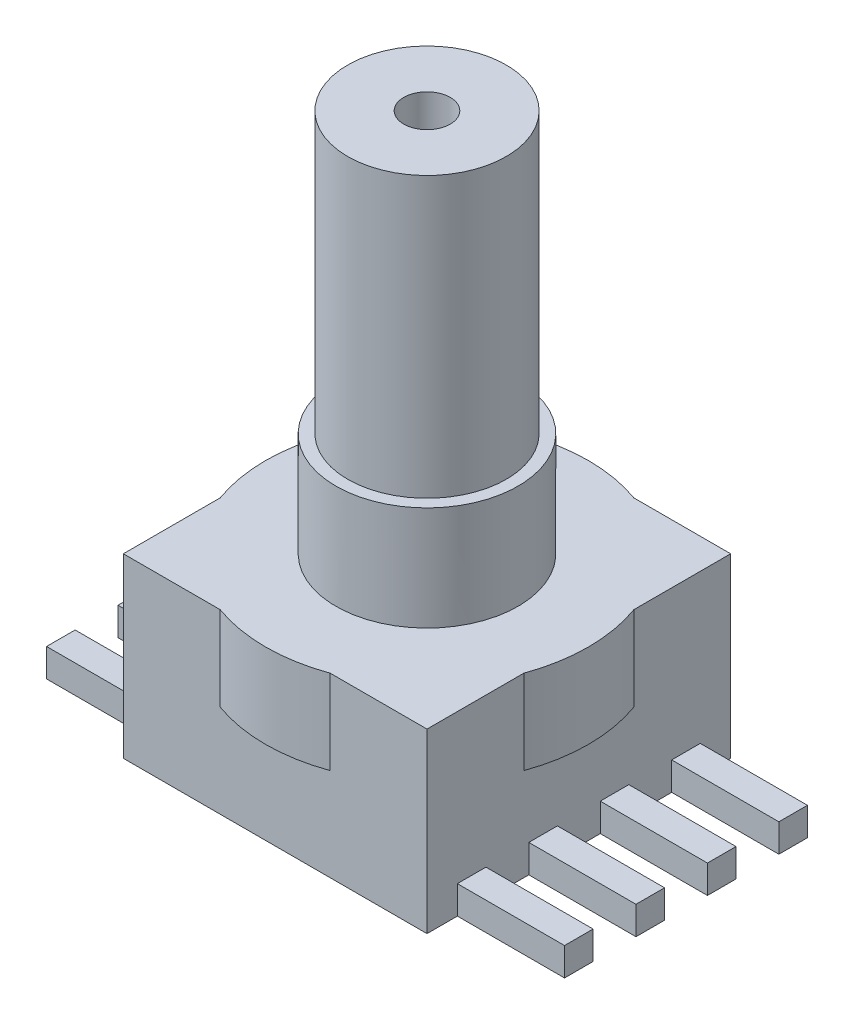
SolidWorks part; units mm, degrees
ref_plane "Front Plane" through (0, 0, 0) normal (0, 0, 1) x (1, 0, 0)
ref_plane "Top Plane" through (0, 0, 0) normal (0, 1, 0) x (1, 0, 0)
ref_plane "Right Plane" through (0, 0, 0) normal (1, 0, 0) x (0, 0, -1)
sketch "Sketch1" plane through (0, 0, 0) normal (0, 1, 0) x (1, 0, 0)
  line L1 (-5.3975, -5.3975) -> (5.3975, -5.3975)
  line L2 (-5.3975, -5.3975) -> (-5.3975, 5.3975)
  line L3 (-5.3975, 5.3975) -> (5.3975, 5.3975)
  line L4 (5.3975, -5.3975) -> (5.3975, 5.3975)
  line L5 (-5.3975, -5.3975) -> (5.3975, 5.3975) construction
  line L6 (-5.3975, 5.3975) -> (5.3975, -5.3975) construction
  point P0 (0, 0)
  dimension "D1" = 10.795
extrude "Boss-Extrude1" add sketch "Sketch1" along normal blind 6.2992
sketch "Sketch3" plane through (0, 6.2992, 0) normal (0, 1, 0) x (1, 0, 0)
  circle A0 centre (0, 0) radius 5.7404
  dimension "D1" = 11.4808
extrude "Boss-Extrude2" add sketch "Sketch3" against normal blind 3
sketch "Sketch4" plane through (0, 0, 0) normal (0, 1, 0) x (1, 0, 0)
  circle A0 centre (0, 0) radius 2.8194
  dimension "D1" = 5.6388
extrude "Boss-Extrude3" add sketch "Sketch4" along normal blind 19.939
sketch "Sketch5" plane through (0, 19.939, 0) normal (0, 1, 0) x (1, 0, 0)
  circle A0 centre (0, 0) radius 0.8255
  dimension "D1" = 1.651
extrude "Cut-Extrude1" cut sketch "Sketch5" against normal blind 15
sketch "Sketch7" plane through (0, 0, 0) normal (0, 1, 0) x (1, 0, 0)
  circle A0 centre (0, 0) radius 3.2385
  dimension "D1" = 6.477
extrude "Boss-Extrude4" add sketch "Sketch7" along normal blind 10
sketch "Sketch8" plane through (0, 0, 0) normal (0, 1, 0) x (1, 0, 0)
  line L0 (0, 0) -> (-7.5534, 0) construction
  line L1 (-9.2075, 4.318) -> (-9.2075, 0) construction
  line L2 (-9.2075, 3.302) -> (-4.8975, 3.302)
  line L3 (-9.2075, 3.302) -> (-9.2075, 4.318)
  line L4 (-9.2075, 4.318) -> (-4.8975, 4.318)
  line L5 (-4.8975, 3.302) -> (-4.8975, 4.318)
  line L6 (-9.2075, 0.762) -> (-4.8975, 0.762)
  line L7 (-9.2075, 0.762) -> (-9.2075, 1.778)
  line L8 (-9.2075, 1.778) -> (-4.8975, 1.778)
  line L9 (-4.8975, 0.762) -> (-4.8975, 1.778)
  line L10 (-9.2075, 1.778) -> (-9.2075, -2.54) construction
  line L11 (-9.2075, -1.778) -> (-4.8975, -1.778)
  line L12 (-9.2075, -1.778) -> (-9.2075, -0.762)
  line L13 (-9.2075, -0.762) -> (-4.8975, -0.762)
  line L14 (-4.8975, -1.778) -> (-4.8975, -0.762)
  line L15 (-9.2075, -0.762) -> (-9.2075, -5.08) construction
  line L16 (-9.2075, -4.318) -> (-4.8975, -4.318)
  line L17 (-9.2075, -4.318) -> (-9.2075, -3.302)
  line L18 (-9.2075, -3.302) -> (-4.8975, -3.302)
  line L19 (-4.8975, -4.318) -> (-4.8975, -3.302)
  line L20 (-9.2075, -3.302) -> (-9.2075, -7.62) construction
  line L22 (-4.8975, 1.778) -> (-4.8975, 0) construction
  line L23 (-4.8975, 0) -> (-4.8975, -1.778) construction
  line L24 (0, 0) -> (0, 3.9869) construction
  line L25 (4.8975, 0) -> (4.8975, -1.778) construction
  line L26 (4.8975, 1.778) -> (4.8975, 0) construction
  line L27 (9.2075, -0.762) -> (9.2075, -5.08) construction
  line L28 (9.2075, 1.778) -> (9.2075, -2.54) construction
  line L29 (9.2075, 4.318) -> (9.2075, 0) construction
  line L30 (4.8975, -4.318) -> (4.8975, -3.302)
  line L31 (9.2075, -3.302) -> (4.8975, -3.302)
  line L32 (9.2075, -4.318) -> (9.2075, -3.302)
  line L33 (9.2075, -4.318) -> (4.8975, -4.318)
  line L34 (4.8975, -1.778) -> (4.8975, -0.762)
  line L35 (9.2075, -0.762) -> (4.8975, -0.762)
  line L36 (9.2075, -1.778) -> (9.2075, -0.762)
  line L37 (9.2075, -1.778) -> (4.8975, -1.778)
  line L38 (4.8975, 0.762) -> (4.8975, 1.778)
  line L39 (9.2075, 1.778) -> (4.8975, 1.778)
  line L40 (9.2075, 0.762) -> (9.2075, 1.778)
  line L41 (9.2075, 0.762) -> (4.8975, 0.762)
  line L42 (4.8975, 3.302) -> (4.8975, 4.318)
  line L43 (9.2075, 4.318) -> (4.8975, 4.318)
  line L44 (9.2075, 3.302) -> (9.2075, 4.318)
  line L45 (9.2075, 3.302) -> (4.8975, 3.302)
  line L46 (-5.3975, 5.3975) -> (-5.3975, 1.9543) construction
  point P45 (0, 0)
  point P46 (-4.2652, 3.9869)
  dimension "D2" = 1.016
  dimension "D3" = 18.415
  dimension "D4" = 2.54
  dimension "D5" = 0.5
  dimension "D1" = 4
extrude "Boss-Extrude5" add sketch "Sketch8" along normal blind 1
